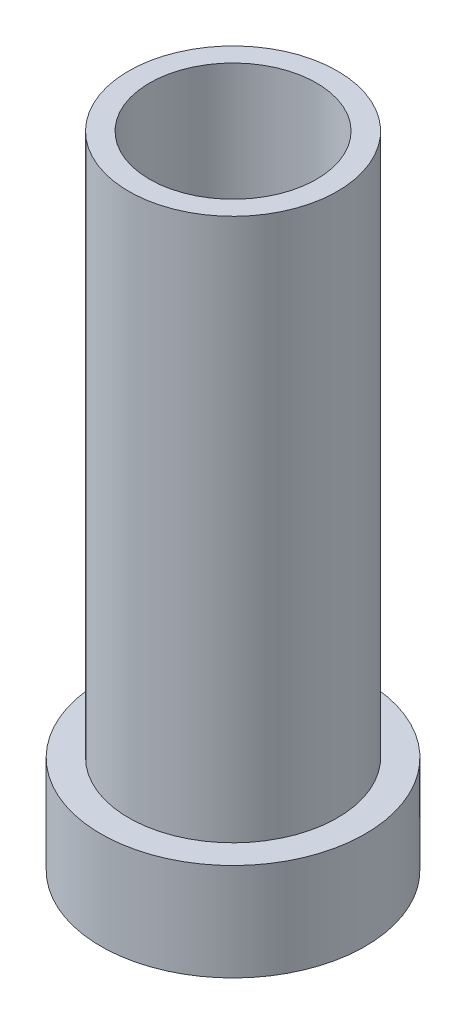
SolidWorks part; units mm, degrees
ref_plane "Спереди" through (0, 0, 0) normal (0, 0, 1) x (1, 0, 0)
ref_plane "Сверху" through (0, 0, 0) normal (0, 1, 0) x (1, 0, 0)
ref_plane "Справа" through (0, 0, 0) normal (1, 0, 0) x (0, 0, -1)
sketch "Эскиз1" plane through (0, 0, 0) normal (0, 0, 1) x (1, 0, 0)
  line L0 (0, 0) -> (0, 23) construction
  line L1 (3.75, 23) -> (3.75, 3.5)
  line L2 (3.75, 3.5) -> (4.75, 3.5)
  line L3 (4.75, 3.5) -> (4.75, 0)
  line L4 (4.75, 0) -> (0, 0)
  line L5 (3.75, 23) -> (0, 23)
  line L6 (0, 0) -> (0, 23)
  dimension "D1" = 9.5
  dimension "D2" = 3.5
  dimension "D3" = 7.5
  dimension "D4" = 1
  dimension "D5" = 23
revolve "Повернуть1" add sketch "Эскиз1" angle 360 about L0
sketch "Эскиз2" plane through (0, 23, 0) normal (0, 1, 0) x (1, 0, 0)
  circle A0 centre (0, 0) radius 3
  dimension "D1" = 6
extrude "Вырез-Вытянуть1" cut sketch "Эскиз2" against normal blind 10
sketch "Эскиз3" plane through (0, 0, 0) normal (0, -1, 0) x (1, 0, 0)
  circle A0 centre (0, 0) radius 2
  dimension "D1" = 4
extrude "Вырез-Вытянуть2" cut sketch "Эскиз3" against normal through all
sketch "Эскиз4" plane through (0, 3.5, 0) normal (0, 1, 0) x (1, 0, 0)
  circle A0 centre (0, 0) radius 3.75 construction
  circle A1 centre (0, 0) radius 4.75
  circle A2 centre (0, 0) radius 4.75
  circle A3 centre (0, 0) radius 3.75
  dimension "D1" = 0
